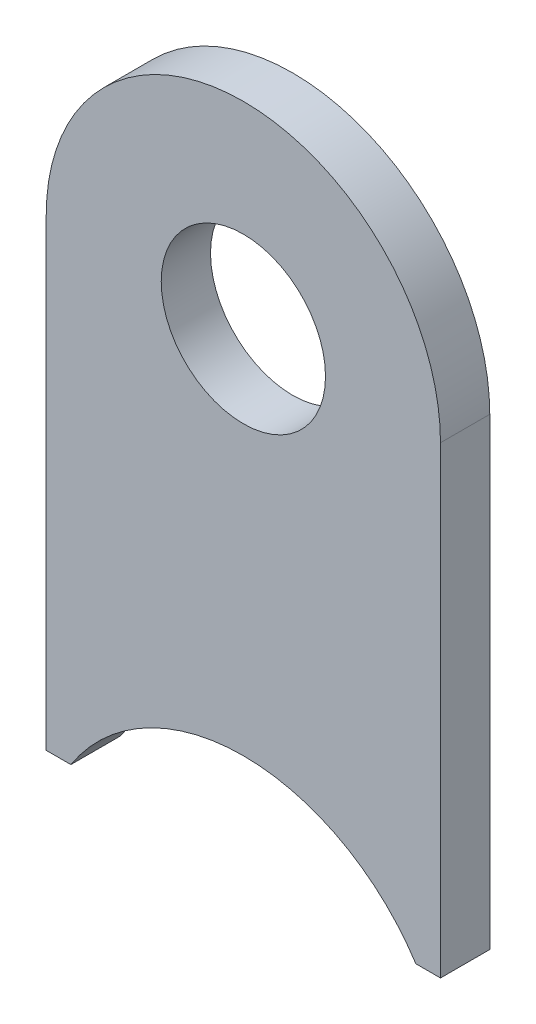
SolidWorks part; units mm, degrees
ref_plane "Płaszczyzna przednia" through (0, 0, 0) normal (0, 0, 1) x (1, 0, 0)
ref_plane "Płaszczyzna górna" through (0, 0, 0) normal (0, 1, 0) x (1, 0, 0)
ref_plane "Płaszczyzna prawa" through (0, 0, 0) normal (1, 0, 0) x (0, 0, -1)
ref_plane "Płaszczyzna1" through (0, 0, -1.5) normal (0, 0, -1) x (-1, 0, 0)
sketch "Szkic1" plane through (0, 0, -1.5) normal (0, 0, -1) x (-1, 0, 0)
  line L0 (-12, 0) -> (-12, -28.2177)
  line L1 (-12, -28.2177) -> (-10.5, -28.2177)
  line L2 (10.5, -28.2177) -> (12, -28.2177)
  line L3 (12, -28.2177) -> (12, 0)
  circle A0 centre (0, 0) radius 5
  arc A1 (-10.5, -28.2177) -> (10.5, -28.2177) centre (0, -35) cw
  arc A2 (12, 0) -> (-12, 0) centre (0, 0) ccw
  dimension "D1" = 10
  dimension "D2" = 12.5
  dimension "D3" = 12
  dimension "D4" = 1.5
  dimension "D5" = 35
extrude "Dodanie-wyciągnięcie1" add sketch "Szkic1" against normal blind 3
